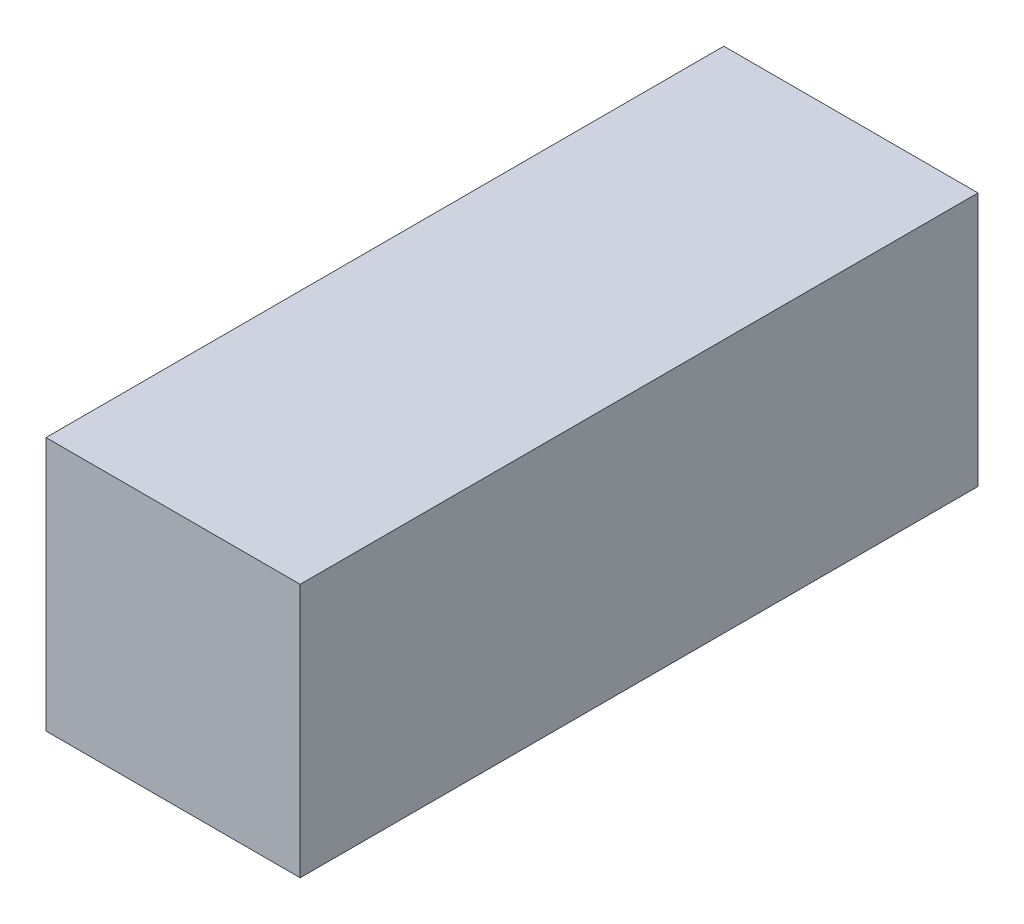
SolidWorks part; units mm, degrees
ref_plane "Front Plane" through (0, 0, 0) normal (0, 0, 1) x (1, 0, 0)
ref_plane "Top Plane" through (0, 0, 0) normal (0, 1, 0) x (1, 0, 0)
ref_plane "Right Plane" through (0, 0, 0) normal (1, 0, 0) x (0, 0, -1)
sketch "Sketch1" plane through (0, 0, 0) normal (0, 0, 1) x (1, 0, 0)
  line L1 (0, 0) -> (300, 0)
  line L2 (0, 0) -> (0, 300)
  line L3 (0, 300) -> (300, 300)
  line L4 (300, 0) -> (300, 300)
  dimension "D1" = 300
  dimension "D2" = 300
extrude "Boss-Extrude1" add sketch "Sketch1" along normal blind 800
